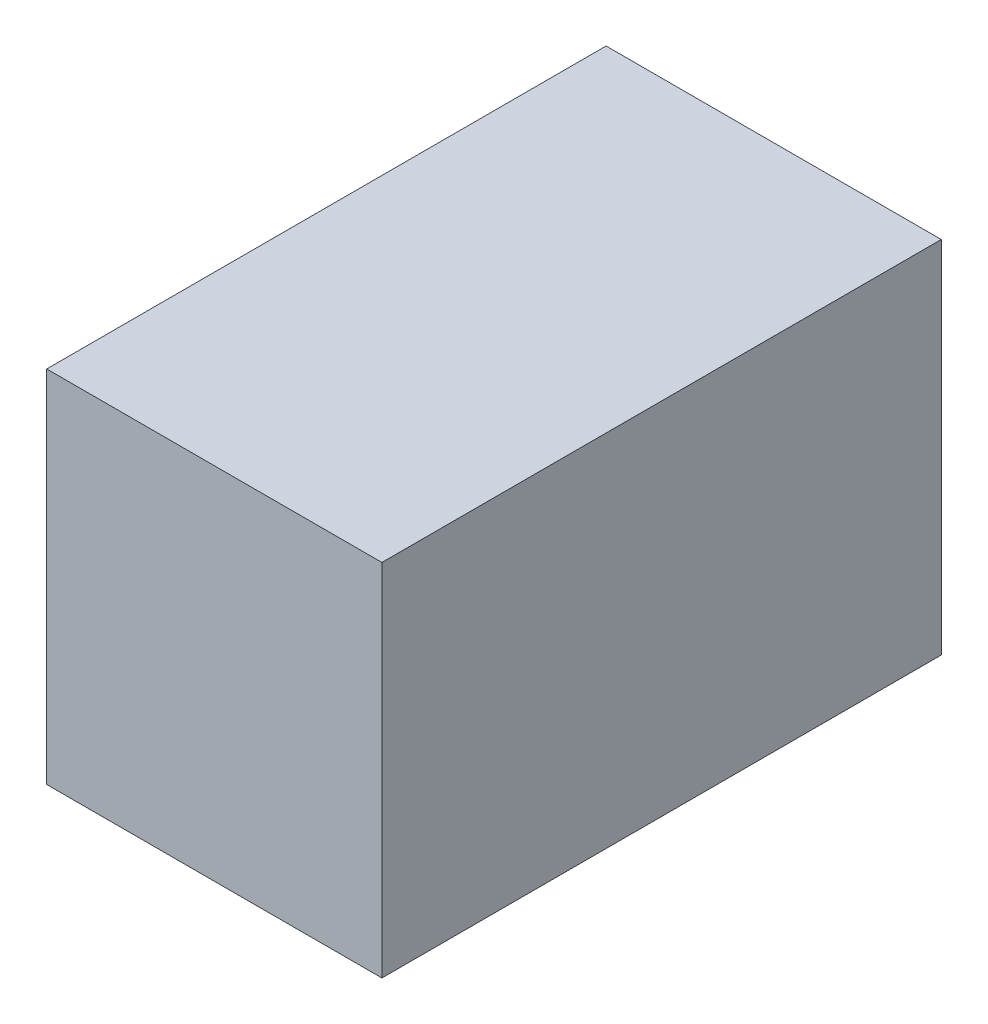
SolidWorks part; units mm, degrees
ref_plane "Front Plane" through (0, 0, 0) normal (0, 0, 1) x (1, 0, 0)
ref_plane "Top Plane" through (0, 0, 0) normal (0, 1, 0) x (1, 0, 0)
ref_plane "Right Plane" through (0, 0, 0) normal (1, 0, 0) x (0, 0, -1)
sketch "Sketch4" plane through (0, 0, 0) normal (1, 0, 0) x (0, 0, -1)
  line L1 (-15.525, 9.275) -> (15.525, 9.275)
  line L2 (-15.525, 9.275) -> (-15.525, -9.275)
  line L3 (-15.525, -9.275) -> (15.525, -9.275)
  line L4 (15.525, 9.275) -> (15.525, -9.275)
  line L5 (-15.525, 9.275) -> (15.525, -9.275) construction
  line L6 (-15.525, -9.275) -> (15.525, 9.275) construction
  point P0 (0, 0)
  dimension "D1" = 31.05
  dimension "D2" = 18.55
extrude "Boss-Extrude1" add sketch "Sketch4" along normal blind 19
shell "Shell1" thickness 2
sketch "Sketch5" plane through (0, 0, -17.525) normal (0, 0, -1) x (-1, 0, 0)
  line L0 (0, -11.275) -> (0, 11.275) construction
  line L1 (0, 9.275) -> (-12, 9.275)
  line L2 (-12, 9.275) -> (-12, -9.275)
  line L3 (-12, -9.275) -> (0, -9.275)
  line L4 (-21, 11.275) -> (0, 11.275) construction
  line L5 (-21, -11.275) -> (0, -11.275) construction
  line L6 (0, 9.275) -> (0, -9.275)
  dimension "D1" = 12
  dimension "D2" = 2
  dimension "D3" = 2
extrude "Cut-Extrude1" cut sketch "Sketch5" against normal up to surface (2 mm away) up to face at (9.5, 0, -15.525)
equation "\"terminalRad\"= 3mm"
equation "\"terminalLen\"= 10.5mm"
equation "\"threadlen\"=11"
